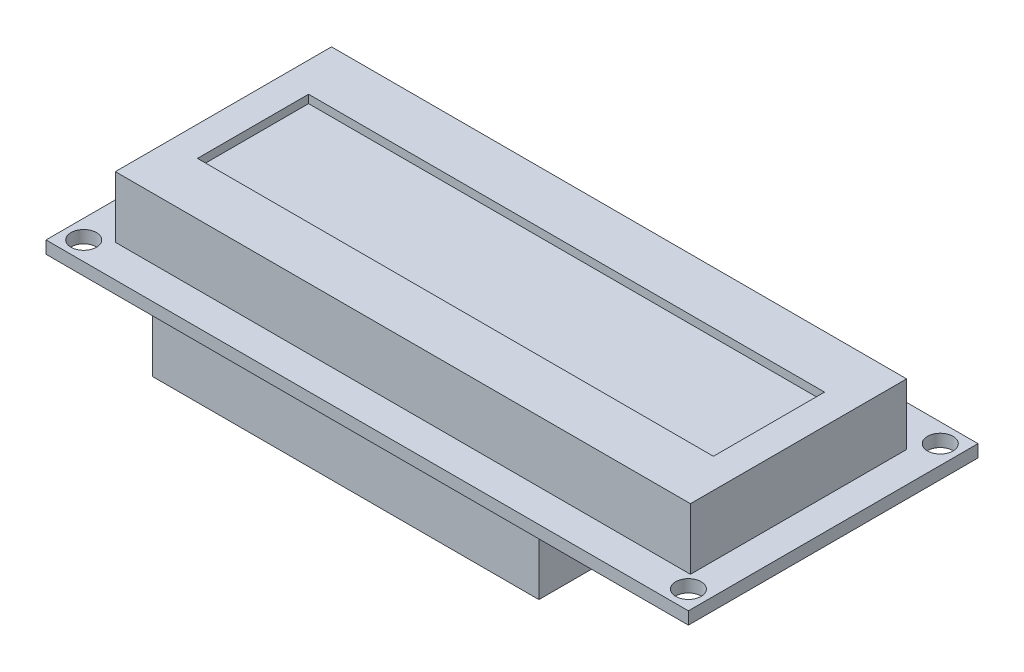
SolidWorks part; units mm, degrees
ref_plane "Front Plane" through (0, 0, 0) normal (0, 0, 1) x (1, 0, 0)
ref_plane "Top Plane" through (0, 0, 0) normal (0, 1, 0) x (1, 0, 0)
ref_plane "Right Plane" through (0, 0, 0) normal (1, 0, 0) x (0, 0, -1)
sketch "Sketch1" plane through (0, 0, 0) normal (0, 1, 0) x (1, 0, 0)
  line L0 (2.3495, 33.7185) -> (77.6605, 33.7185) construction
  line L1 (0, 0) -> (80.01, 0)
  line L2 (0, 0) -> (0, 36.068)
  line L3 (0, 36.068) -> (80.01, 36.068)
  line L4 (80.01, 0) -> (80.01, 36.068)
  line L5 (77.6605, 33.7185) -> (77.6605, 2.3495) construction
  line L7 (2.3495, 2.3495) -> (77.6605, 2.3495) construction
  line L8 (2.3495, 2.3495) -> (2.3495, 33.7185) construction
  line L9 (75.311, 0) -> (155.321, 0) construction
  line L10 (75.311, 31.369) -> (155.321, 31.369) [skipped]
  line L11 (0, 31.369) -> (80.01, 31.369) [skipped]
  circle A0 centre (2.3495, 2.3495) radius 1.5875
  circle A1 centre (77.6605, 2.3495) radius 1.5875
  circle A2 centre (77.6605, 33.7185) radius 1.5875
  circle A3 centre (2.3495, 33.7185) radius 1.5875
  dimension "D3" = 3.175
  dimension "D1" = 80.01
  dimension "D2" = 36.068
  dimension "D4" = 2.3495
  dimension "D5" = 2.3495
  dimension "D8" = 75.311
  dimension "D9" = 31.369
  dimension "D6" = 2
  dimension "D7" = 2
extrude "PCB" add sketch "Sketch1" along normal blind 1.5494
sketch "Sketch2" plane through (0, 1.5494, 0) normal (0, 1, 0) x (1, 0, 0)
  line L0 (0, 0) -> (80.01, 0) construction
  line L1 (4.572, 4.064) -> (76.2, 4.064)
  line L2 (4.572, 4.064) -> (4.572, 30.988)
  line L3 (4.572, 30.988) -> (76.2, 30.988)
  line L4 (76.2, 4.064) -> (76.2, 30.988)
  line L5 (0, 36.068) -> (0, 0) construction
  dimension "D1" = 71.628
  dimension "D2" = 26.924
  dimension "D3" = 4.064
  dimension "D4" = 4.572
extrude "Boss-Extrude2" add sketch "Sketch2" along normal blind 7.62
sketch "Sketch3" plane through (0, 9.1694, 0) normal (0, 1, 0) x (1, 0, 0)
  line L1 (8.255, 10.6045) -> (72.517, 10.6045)
  line L2 (8.255, 10.6045) -> (8.255, 24.4475)
  line L3 (8.255, 24.4475) -> (72.517, 24.4475)
  line L4 (72.517, 10.6045) -> (72.517, 24.4475)
  line L6 (40.386, 10.6045) -> (40.386, 4.064) construction
  line L7 (4.572, 4.064) -> (76.2, 4.064) construction
  line L8 (4.572, 17.526) -> (8.255, 17.526) construction
  line L9 (4.572, 30.988) -> (4.572, 4.064) construction
  dimension "D1" = 64.262
  dimension "D2" = 13.843
extrude "Screen" cut sketch "Sketch3" against normal blind 1.016
sketch "Sketch4" plane through (0, 0, 0) normal (0, -1, 0) x (1, 0, 0)
  line L0 (0, -36.068) -> (0, 0) construction
  line L1 (54.483, -35.56) -> (6.35, -35.56)
  line L2 (54.483, -35.56) -> (54.483, -6.9088)
  line L3 (54.483, -6.9088) -> (6.35, -6.9088)
  line L4 (6.35, -35.56) -> (6.35, -6.9088)
  line L5 (80.01, -36.068) -> (0, -36.068) construction
  dimension "D1" = 48.133
  dimension "D2" = 28.6512
  dimension "D3" = 6.35
  dimension "D4" = 0.508
extrude "Circuits" add sketch "Sketch4" along normal blind 13.462
sketch "Sketch5" plane through (0, -13.462, 0) normal (0, -1, 0) x (1, 0, 0)
  line L0 (54.483, -6.9088) -> (6.35, -6.9088) construction
  line L1 (8.6995, -18.9611) -> (8.0645, -18.9611)
  line L2 (8.6995, -18.9611) -> (8.6995, -18.3261)
  line L3 (8.6995, -18.3261) -> (8.0645, -18.3261)
  line L4 (8.0645, -18.9611) -> (8.0645, -18.3261)
  line L5 (8.6995, -18.9611) -> (8.0645, -18.3261) construction
  line L6 (8.6995, -18.3261) -> (8.0645, -18.9611) construction
  line L7 (6.35, -6.9088) -> (6.35, -35.56) construction
  line L8 (8.6995, -21.5011) -> (8.0645, -21.5011)
  line L9 (8.6995, -21.5011) -> (8.6995, -20.8661)
  line L10 (8.6995, -20.8661) -> (8.0645, -20.8661)
  line L11 (8.0645, -21.5011) -> (8.0645, -20.8661)
  line L12 (8.6995, -21.5011) -> (8.0645, -20.8661) construction
  line L13 (8.6995, -20.8661) -> (8.0645, -21.5011) construction
  line L14 (8.6995, -24.0411) -> (8.0645, -24.0411)
  line L15 (8.6995, -24.0411) -> (8.6995, -23.4061)
  line L16 (8.6995, -23.4061) -> (8.0645, -23.4061)
  line L17 (8.0645, -24.0411) -> (8.0645, -23.4061)
  line L18 (8.6995, -24.0411) -> (8.0645, -23.4061) construction
  line L19 (8.6995, -23.4061) -> (8.0645, -24.0411) construction
  point P0 (8.382, -18.6436)
  point P10 (8.382, -21.1836)
  point P15 (8.382, -23.7236)
  dimension "D1" = 11.7348
  dimension "D2" = 2.032
  dimension "D3" = 0.635
  dimension "D4" = 0.635
  dimension "D5" = 3
extrude "Pins" add sketch "Sketch5" along normal blind 2.54
equation "\"D4@Sketch1\"=\"D3@Sketch1\"/2+.03"
equation "\"D5@Sketch1\"=\"D4@Sketch1\""
equation "\"D9@Sketch1\"=\"D2@Sketch1\"-\"D5@Sketch1\"*2"
equation "\"D8@Sketch1\"=\"D1@Sketch1\"-\"D4@Sketch1\"*2"
equation "\"D4@Sketch5\"=\"D3@Sketch5\""
